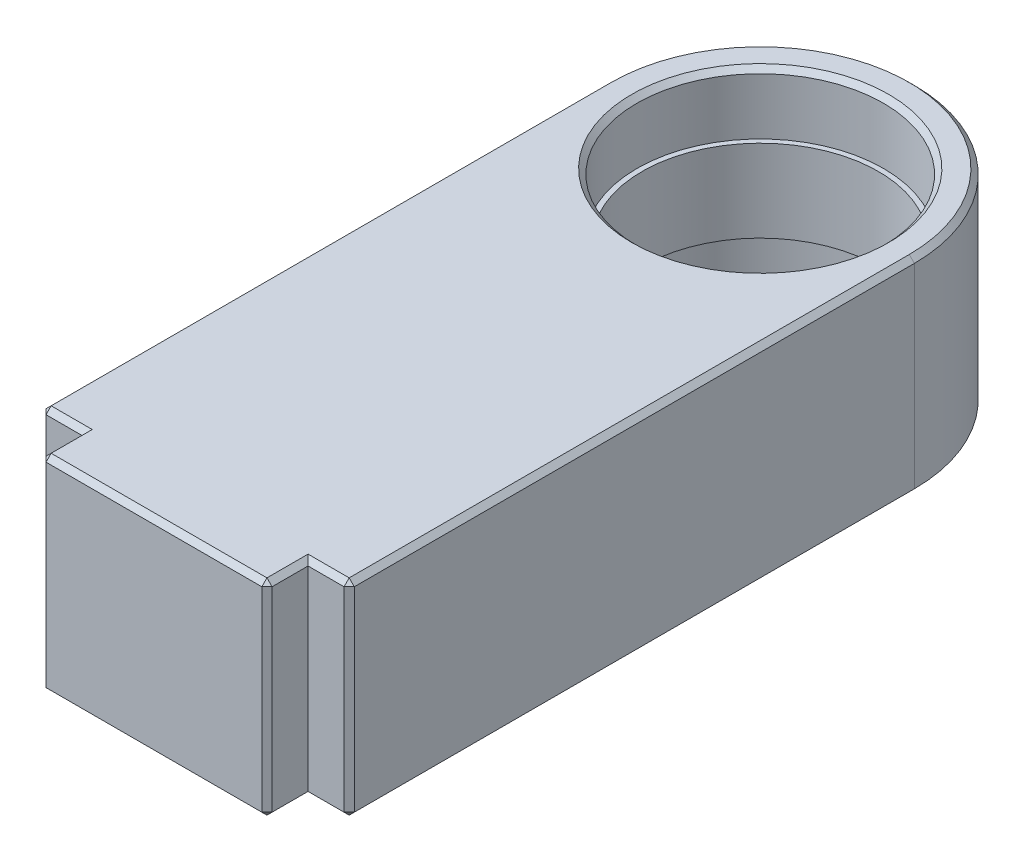
SolidWorks part; units mm, degrees
ref_plane "Front Plane" through (0, 0, 0) normal (0, 0, 1) x (1, 0, 0)
ref_plane "Top Plane" through (0, 0, 0) normal (0, 1, 0) x (1, 0, 0)
ref_plane "Right Plane" through (0, 0, 0) normal (1, 0, 0) x (0, 0, -1)
sketch "Sketch1" plane through (0, 0, 0) normal (0, 1, 0) x (1, 0, 0)
  line L0 (0, 0) -> (0, -55) construction
  line L1 (15, -55) -> (-15, -55)
  line L2 (-15, -55) -> (-15, 0)
  line L3 (15, -55) -> (15, 0)
  circle A0 centre (0, 0) radius 12
  arc A1 (15, 0) -> (-15, 0) centre (0, 0) ccw
  dimension "D1" = 24
  dimension "D2" = 30
  dimension "D3" = 55
extrude "Boss-Extrude1" add sketch "Sketch1" along normal mid plane 20
sketch "Sketch2" plane through (0, 0, 0) normal (0, 1, 0) x (1, 0, 0)
  circle A0 centre (0, 0) radius 12 construction
  circle A1 centre (0, 0) radius 12
  circle A2 centre (0, 0) radius 11.5
  dimension "D1" = 0.5
extrude "Boss-Extrude2" add sketch "Sketch2" along normal mid plane 8
sketch "Sketch3" plane through (0, 0, 55) normal (0, 0, 1) x (1, 0, 0)
  line L0 (-15, 10) -> (15, 10) construction
  line L1 (11, -10) -> (-11, -10)
  line L2 (11, -10) -> (11, 10)
  line L3 (11, 10) -> (-11, 10)
  line L4 (-11, -10) -> (-11, 10)
  line L5 (11, -10) -> (-11, 10) construction
  line L6 (11, 10) -> (-11, -10) construction
  point P0 (0, 0)
  dimension "D1" = 22
extrude "Boss-Extrude3" add sketch "Sketch3" along normal blind 4
chamfer "Chamfer2" distance 0.5 angle 45 22 edges at (0, 10, 12) (0, -10, 12) (13, 10, 55) (11, 10, 57) (0, 10, 59) (-11, 10, 57) (-13, 10, 55) (-15, 10, 27.5) (0, 10, -15) (15, 10, 27.5) (0, -10, -15) (-15, -10, 27.5) (-15, 0, 55) (-13, -10, 55) (-11, -10, 57) (15, -10, 27.5) (15, 0, 55) (13, -10, 55) (11, -10, 57) (11, 0, 59) (0, -10, 59) (-11, 0, 59)
